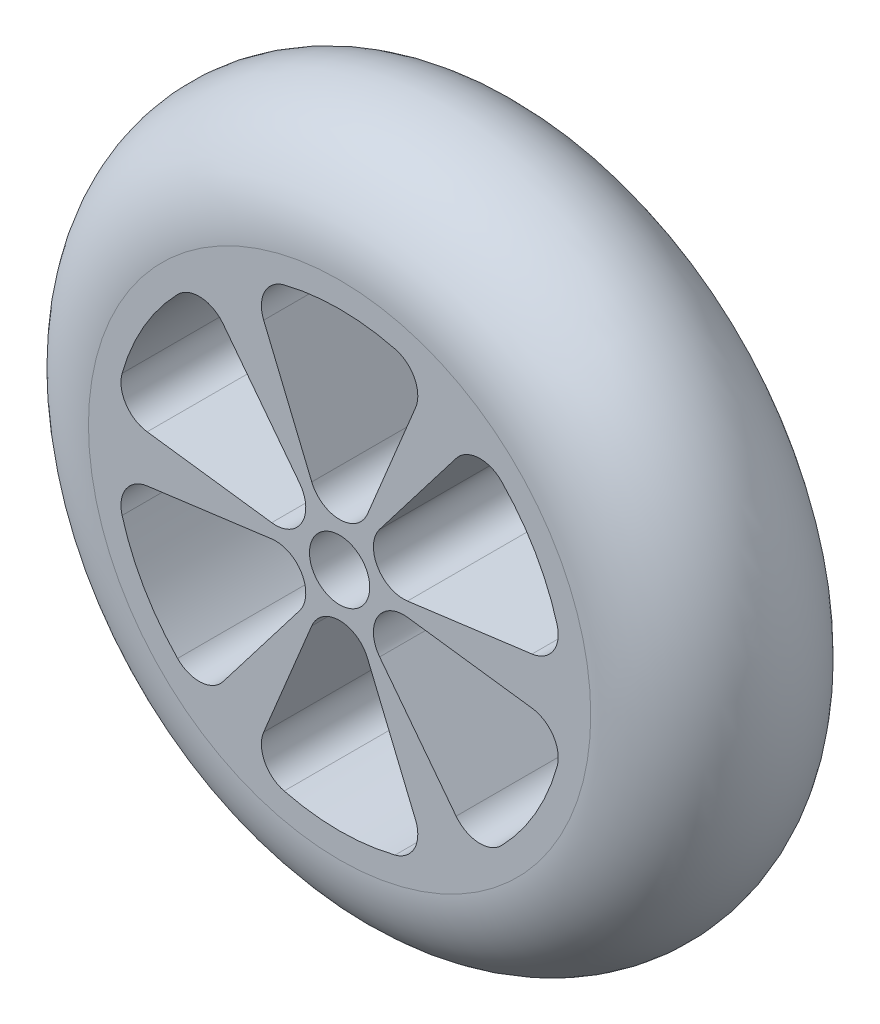
SolidWorks part; units mm, degrees
ref_plane "Front Plane" through (0, 0, 0) normal (0, 0, 1) x (1, 0, 0)
ref_plane "Top Plane" through (0, 0, 0) normal (0, 1, 0) x (1, 0, 0)
ref_plane "Right Plane" through (0, 0, 0) normal (1, 0, 0) x (0, 0, -1)
sketch "Sketch5" plane through (0, 0, 0) normal (0, 0, 1) x (1, 0, 0)
  circle A0 centre (0, 0) radius 6
  circle A1 centre (0, 0) radius 50
  dimension "D1" = 12
  dimension "D2" = 100
extrude "Boss-Extrude2" add sketch "Sketch5" along normal blind 40
ref_axis "Axis2" through (0, 0, 40) along (0, 0, -1)
sketch "Sketch7" plane through (0, 0, 0) normal (1, 0, 0) x (0, 0, -1)
  line L0 (-40, 50) -> (0, 50)
  arc A0 (0, 50) -> (-40, 50) centre (-20, 50) ccw
revolve "Revolve3" add sketch "Sketch7" angle 360 about axis through (0, 0, 40) along (0, 0, -1)
sketch "Sketch8" plane through (0, 0, 40) normal (0, 0, 1) x (1, 0, 0)
  line L0 (0, -0.9758) -> (0, 32.573) construction
  line L1 (5.5433, 12.4068) -> (15.1135, 35.5114)
  line L2 (-5.5433, 12.4068) -> (-15.1135, 35.5114)
  circle A3 centre (0, 0) radius 45
  arc A4 (11.0426, 43.6241) -> (-11.0426, 43.6241) centre (0, 0) ccw
  arc A6 (-11.0426, 43.6241) -> (-15.1135, 35.5114) centre (-9.5702, 37.8075) ccw
  arc A7 (-5.5433, 12.4068) -> (5.5433, 12.4068) centre (0, 14.7029) ccw
  arc A8 (15.1135, 35.5114) -> (11.0426, 43.6241) centre (9.5702, 37.8075) ccw
  dimension "D3" = 6
  dimension "D2" = 45
  dimension "D1" = 5
extrude "Cut-Extrude1" cut sketch "Sketch8" against normal through all
pattern_circular "CirPattern1" count 6 over 360 about axis through (0, 0, 0) along (0, 0, 1) of "Cut-Extrude1"
